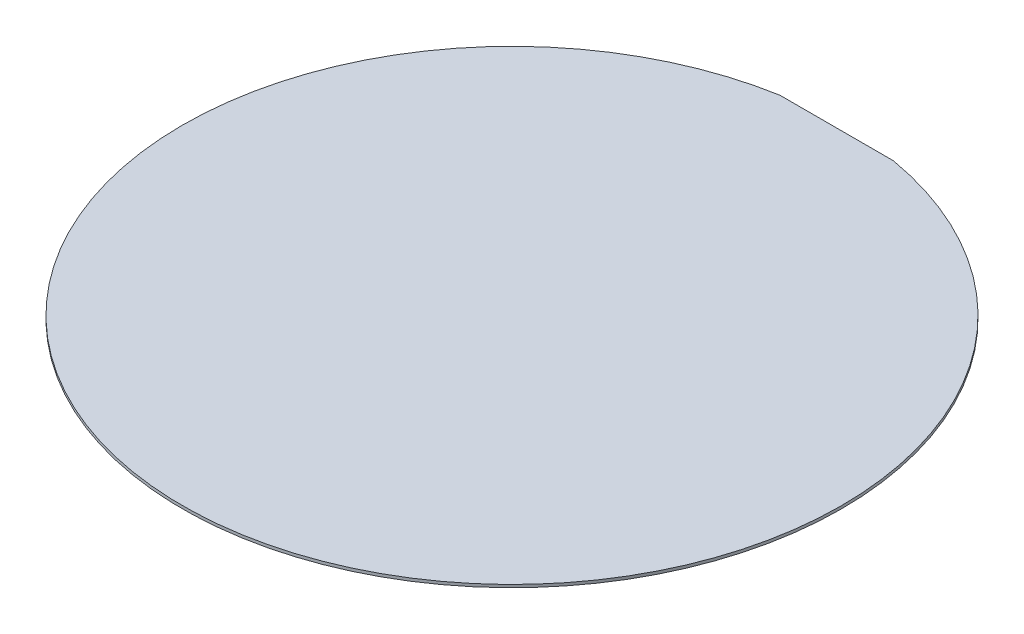
SolidWorks part; units mm, degrees
material "AISI 316 Stainless Steel Sheet (SS)"
ref_plane "Front Plane" through (0, 0, 0) normal (0, 0, 1) x (1, 0, 0)
ref_plane "Top Plane" through (0, 0, 0) normal (0, 1, 0) x (1, 0, 0)
ref_plane "Right Plane" through (0, 0, 0) normal (1, 0, 0) x (0, 0, -1)
sketch "Sketch2" plane through (0, 0, 0) normal (0, 1, 0) x (1, 0, 0)
  line L1 (-30.1304, 172.3867) -> (30.1304, 172.3867)
  arc A1 (-30.1304, 172.3867) -> (30.1304, 172.3867) centre (0, 0) ccw
extrude "Boss-Extrude1" add sketch "Sketch2" along normal blind 1.5
